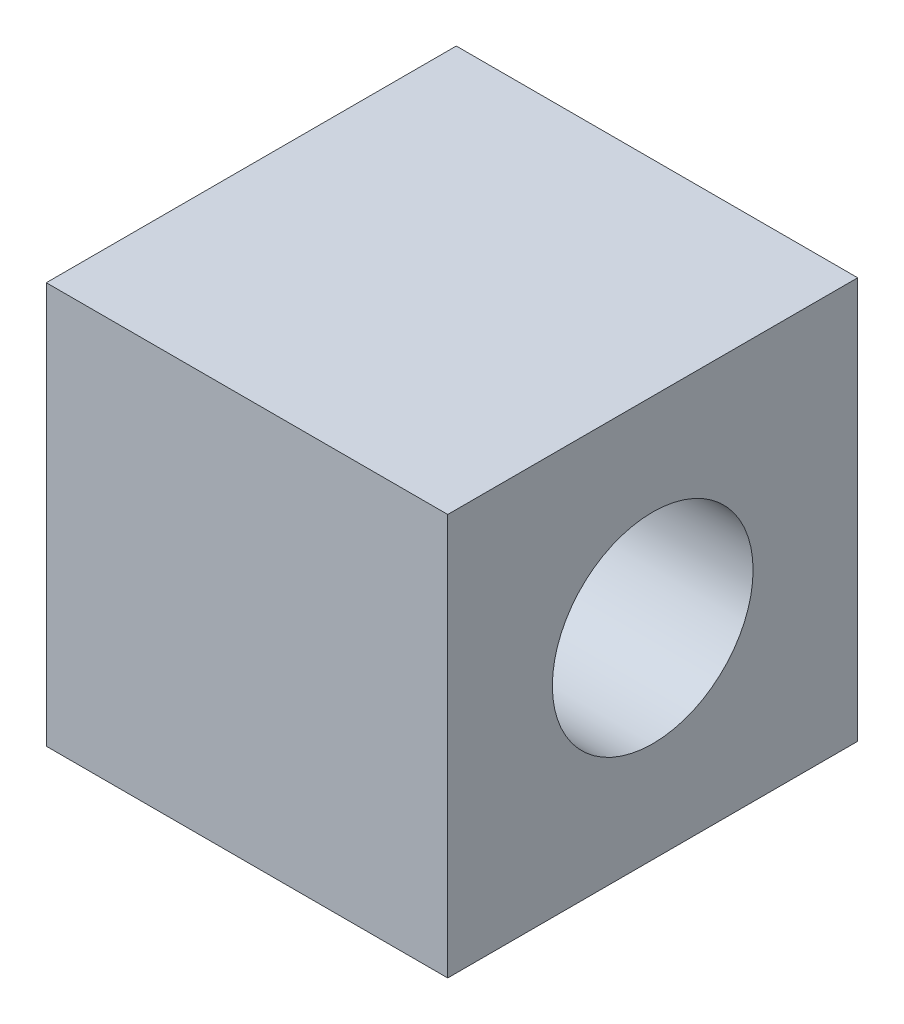
SolidWorks part; units mm, degrees
ref_plane "前视基准面" through (0, 0, 0) normal (0, 0, 1) x (1, 0, 0)
ref_plane "上视基准面" through (0, 0, 0) normal (0, 1, 0) x (1, 0, 0)
ref_plane "右视基准面" through (0, 0, 0) normal (1, 0, 0) x (0, 0, -1)
sketch "草图1" plane through (0, 0, 0) normal (1, 0, 0) x (0, 0, -1)
  line L1 (-5.1065, -5) -> (5.1065, -5)
  line L2 (-5.1065, -5) -> (-5.1065, 5)
  line L3 (-5.1065, 5) -> (5.1065, 5)
  line L4 (5.1065, -5) -> (5.1065, 5)
  line L5 (-5.1065, -5) -> (5.1065, 5) construction
  line L6 (-5.1065, 5) -> (5.1065, -5) construction
  circle A0 centre (0, 0) radius 2.5
  dimension "D1" = 5
  dimension "D2" = 10
extrude "凸台-拉伸1" add sketch "草图1" along normal blind 10
